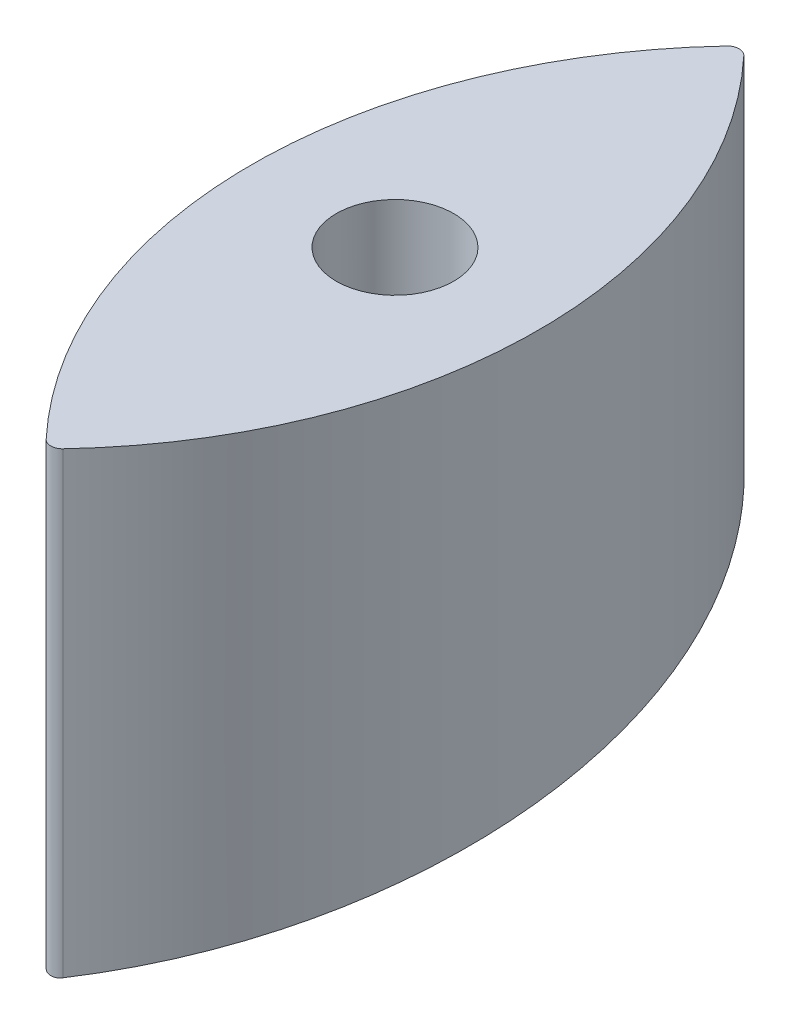
SolidWorks part; units mm, degrees
ref_plane "Front Plane" through (0, 0, 0) normal (0, 0, 1) x (1, 0, 0)
ref_plane "Top Plane" through (0, 0, 0) normal (0, 1, 0) x (1, 0, 0)
ref_plane "Right Plane" through (0, 0, 0) normal (1, 0, 0) x (0, 0, -1)
sketch "Sketch2" plane through (0, 0, 0) normal (1, 0, 0) x (0, 0, -1)
  line L0 (-15.7391, 19.787) -> (12.7788, 17.9806) construction
  line L1 (-38.1, -5.6011) -> (-38.1, 45.1989)
  line L2 (-38.1, 45.1989) -> (38.1, 45.1989)
  line L3 (38.1, 45.1989) -> (38.1, 3.7982)
  spline S0 degree 2 poles (-38.1, -5.6011) (-0.2189, 0.8745) (38.1, 3.7982) knots 0 0 0 1 1 1
  point P4 (0, -3.7491)
  point P8 (0, 0)
  point P9 (0, 0)
  point P11 (0, 0)
  point P13 (-38.1, -5.6011)
  point P14 (38.1, 3.7982)
  point P15 (0, 0)
  point P16 (0, 0)
  point P17 (0, 0)
  dimension "D1" = 28.575
  dimension "D3" = 50.8
  dimension "D4" = 76.2
extrude "Boss-Extrude1" add sketch "Sketch2" against normal mid plane 31.75
sketch "Sketch3" plane through (0, 45.1989, 0) normal (0, 1, 0) x (1, 0, 0)
  line L0 (-15.875, 38.1) -> (-15.875, -38.1) construction
  line L1 (0, 0) -> (0, 38.1) construction
  line L2 (-15.875, 38.1) -> (15.875, 38.1) construction
  line L3 (15.875, 38.1) -> (15.875, -38.1) construction
  line L4 (-15.875, -38.1) -> (15.875, -38.1) construction
  line L9 (15.875, -38.1) -> (15.875, 38.1)
  line L10 (15.875, 38.1) -> (-15.875, 38.1)
  line L11 (-15.875, 38.1) -> (-15.875, -38.1)
  line L12 (-15.875, -38.1) -> (15.875, -38.1)
  line L13 (15.875, -38.1) -> (15.875, 38.1)
  line L14 (15.875, 38.1) -> (-15.875, 38.1)
  line L15 (-15.875, 38.1) -> (-15.875, -38.1)
  line L16 (-15.875, -38.1) -> (15.875, -38.1)
  arc A0 (-0.9249, 37.7004) -> (-0.9249, -37.7004) centre (39.1353, 0) ccw
  arc A1 (0.9249, 37.7004) -> (0.9249, -37.7004) centre (-39.1353, 0) cw
  arc A2 (0.9249, 37.7004) -> (-0.9249, 37.7004) centre (0, 36.83) ccw
  arc A3 (0.9249, -37.7004) -> (-0.9249, -37.7004) centre (0, -36.83) cw
  circle A4 centre (0, 0) radius 6.5
  dimension "D1" = 1.27
  dimension "D3" = 13
  dimension "D2" = 0
extrude "Cut-Extrude1" cut sketch "Sketch3" against normal through all
